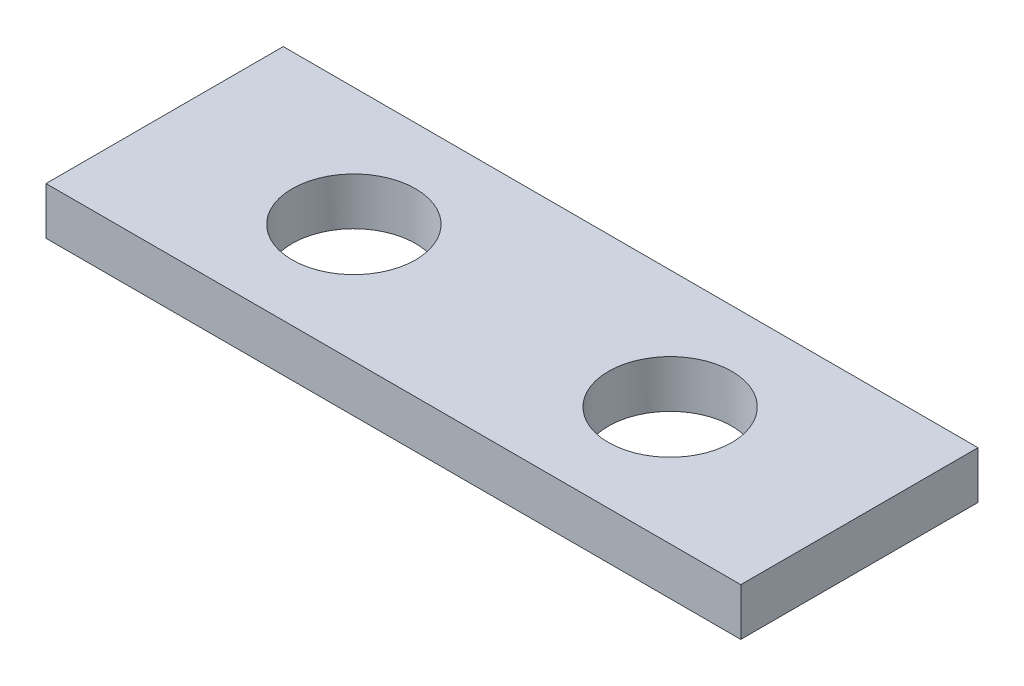
SolidWorks part; units mm, degrees
ref_plane "Front Plane" through (0, 0, 0) normal (0, 0, 1) x (1, 0, 0)
ref_plane "Top Plane" through (0, 0, 0) normal (0, 1, 0) x (1, 0, 0)
ref_plane "Right Plane" through (0, 0, 0) normal (1, 0, 0) x (0, 0, -1)
sketch "Sketch1" plane through (0, 0, 0) normal (0, 1, 0) x (1, 0, 0)
  line L1 (-21.965, -7.5) -> (21.965, -7.5)
  line L2 (-21.965, -7.5) -> (-21.965, 7.5)
  line L3 (-21.965, 7.5) -> (21.965, 7.5)
  line L4 (21.965, -7.5) -> (21.965, 7.5)
  line L5 (-21.965, -7.5) -> (21.965, 7.5) construction
  line L6 (-21.965, 7.5) -> (21.965, -7.5) construction
  point P0 (0, 0)
  dimension "D1" = 43.93
  dimension "D2" = 15
extrude "Boss-Extrude1" add sketch "Sketch1" along normal blind 3
sketch "Sketch2" plane through (0, 3, 0) normal (0, 1, 0) x (1, 0, 0)
  circle A0 centre (-10, 0) radius 3.9
  dimension "D2" = 7.8
  dimension "D1" = 10
extrude "Cut-Extrude1" cut sketch "Sketch2" against normal through all both and the other way through all
mirror "Mirror1" about plane through (0, 0, 0) normal (1, 0, 0) of "Cut-Extrude1"
